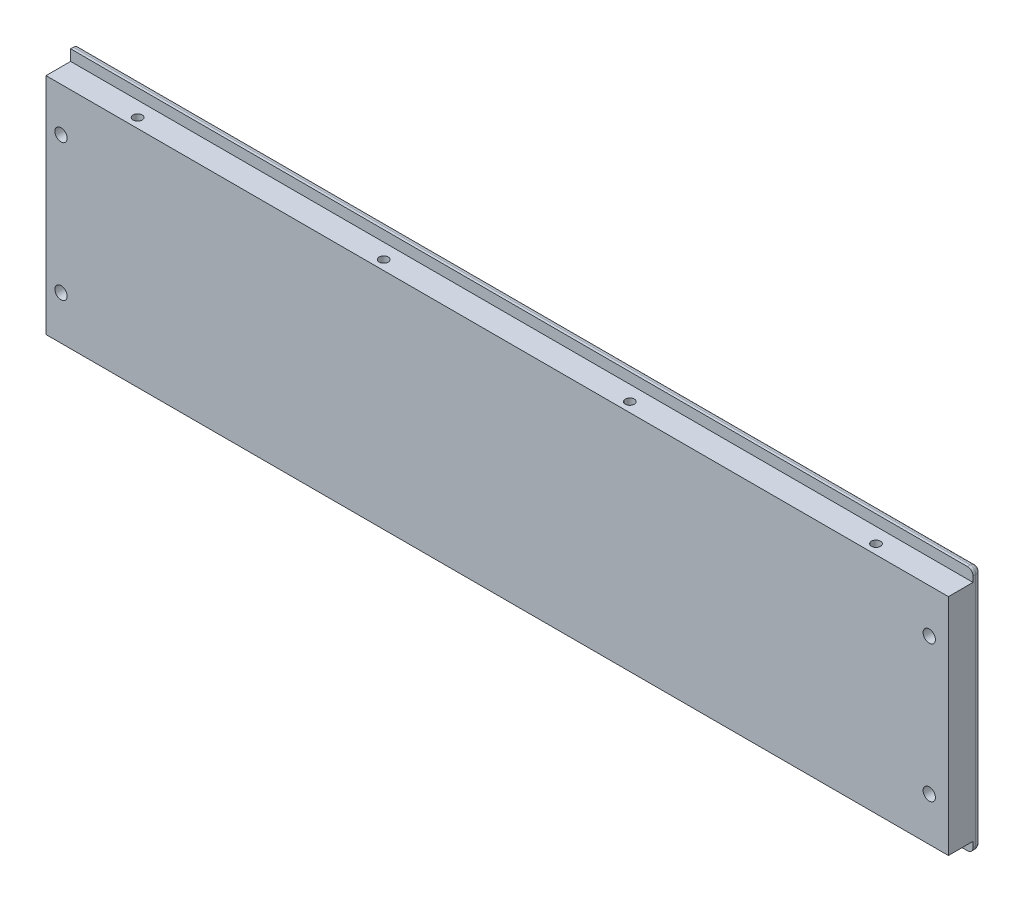
SolidWorks part; units mm, degrees
material "3.3523 (EN-AW 5052)"
ref_plane "前基準面" through (0, 0, 0) normal (0, 0, 1) x (1, 0, 0)
ref_plane "上基準面" through (0, 0, 0) normal (0, 1, 0) x (1, 0, 0)
ref_plane "右基準面" through (0, 0, 0) normal (1, 0, 0) x (0, 0, -1)
sketch "草圖1" plane through (0, 0, 0) normal (0, 0, 1) x (1, 0, 0)
  line L1 (0, 0) -> (330, 0)
  line L2 (0, 0) -> (0, 90)
  line L3 (0, 90) -> (330, 90)
  line L4 (330, 0) -> (330, 90)
  dimension "D1" = 90
  dimension "D2" = 330
extrude "填料-伸長1" add sketch "草圖1" along normal blind 12
sketch "草圖2" plane through (0, 0, 0) normal (-1, 0, 0) x (0, 0, 1)
  line L1 (12, 90) -> (3, 90)
  line L2 (12, 90) -> (12, 86)
  line L3 (12, 86) -> (3, 86)
  line L4 (3, 90) -> (3, 86)
  line L5 (12, 0) -> (3, 0)
  line L6 (12, 0) -> (12, 4)
  line L7 (12, 4) -> (3, 4)
  line L8 (3, 0) -> (3, 4)
  dimension "D1" = 9
  dimension "D2" = 9
  dimension "D3" = 4
  dimension "D4" = 4
extrude "除料-伸長1" cut sketch "草圖2" against normal through all
fillet "圓角1" radius 2 2 edges at (165, 0, 0) (165, 90, 0)
fillet "圓角2" radius 2 5 edges at (330, 90, 2.5) (330, 89.4142, 0.5858) (330, 45, 0) (330, 0.5858, 0.5858) (330, 0, 2.5)
hole_wizard "M4 螺紋孔1" positions "草圖3" profile "草圖4" tap size "M4" standard "ISO" end condition through all
sketch "草圖3" plane through (0, 86, 0) normal (0, 1, 0) x (1, 0, 0)
  line L0 (0, -7.5) -> (330, -7.5) construction
  line L1 (0, -3) -> (0, -12) construction
  line L2 (330, -3) -> (330, -12) construction
  point P0 (30, -8.5)
  point P2 (120, -8.5)
  point P4 (210, -8.5)
  point P6 (300, -8.5)
  dimension "D1" = 1
  dimension "D2" = 90
  dimension "D3" = 90
  dimension "D4" = 90
  dimension "D5" = 30
cosmetic thread "鑽孔螺紋1" parameters "D2"=4
cosmetic thread "鑽孔螺紋2" parameters "D2"=4
cosmetic thread "鑽孔螺紋3" parameters "D2"=4
cosmetic thread "鑽孔螺紋4" parameters "D2"=4
sketch "草圖4" plane through (30, 86, 8.5) normal (1, 0, 0) x (0, 0, 1)
  line L0 (0, 0) -> (0, 86)
  line L1 (0, 86) -> (1.65, 86)
  line L2 (1.65, 86) -> (1.65, 0)
  line L5 (1.65, 0) -> (0, 0)
  line L11 (0, -6.35) -> (0, 107.95) construction
  dimension "貫穿螺孔鑽直徑" = 3.3
  dimension "貫穿螺孔鑽深度" = 86
hole_wizard "M4 錐坑平頭螺釘的錐孔1" positions "草圖7" profile "草圖8" countersink size "M4" standard "ISO" end condition through all
sketch "草圖7" plane through (0, 0, 0) normal (0, 0, -1) x (-1, 0, 0)
  line L0 (-330, 0) -> (-330, 90) construction
  line L1 (0, 0) -> (-330, 0) construction
  line L2 (-330, 90) -> (0, 90) construction
  line L3 (0, 88) -> (0, 2) construction
  point P0 (-323, 20)
  point P2 (-323, 70)
  point P4 (-5.5, 20)
  point P6 (-5.5, 70)
  dimension "D1" = 7
  dimension "D2" = 20
  dimension "D3" = 20
  dimension "D4" = 5.5
sketch "草圖8" plane through (323, 20, 0) normal (1, 0, 0) x (0, 1, 0)
  line L0 (0, 0) -> (0, 12)
  line L1 (0, 12) -> (2.25, 12)
  line L2 (2.25, 12) -> (2.25, 2.45)
  line L3 (2.25, 2.45) -> (4.7, 0)
  line L5 (4.7, 0) -> (0, 0)
  line L6 (-2.25, 2.45) -> (-4.7, 0) construction
  line L11 (0, -6.35) -> (0, 107.95) construction
  dimension "貫穿孔直徑" = 4.5
  dimension "貫穿孔深度" = 12
  dimension "近端錐孔直徑" = 9.4
  dimension "近端錐孔角度" = 90
